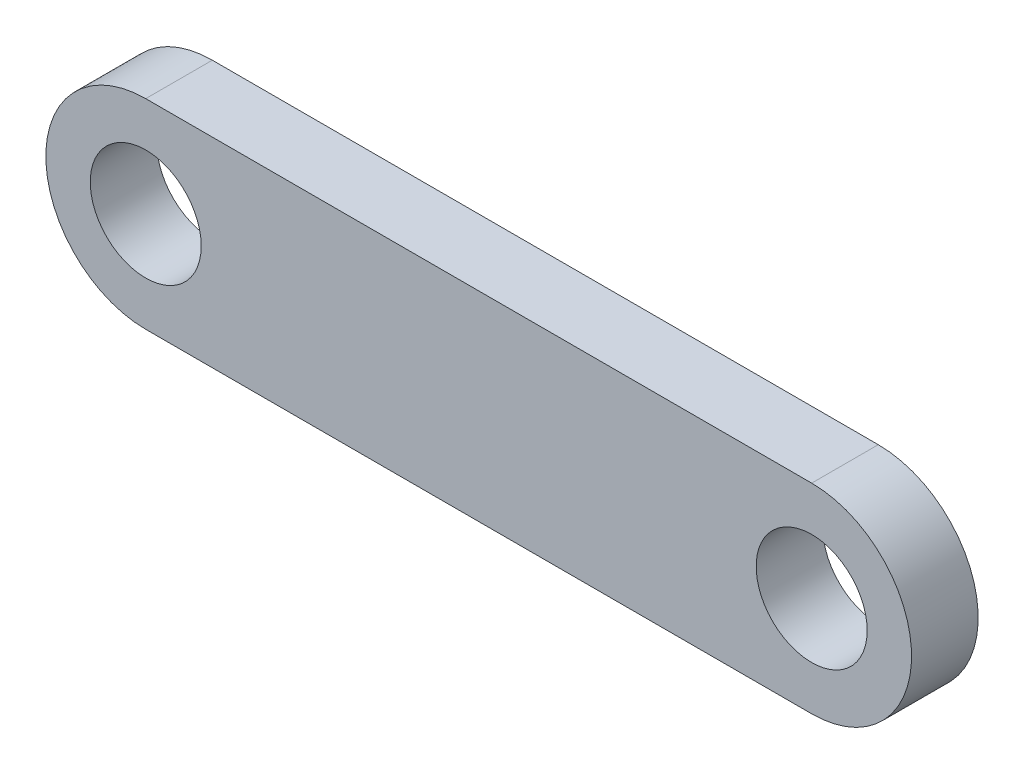
SolidWorks part; units mm, degrees
ref_plane "Alzado" through (0, 0, 0) normal (0, 0, 1) x (1, 0, 0)
ref_plane "Planta" through (0, 0, 0) normal (0, 1, 0) x (1, 0, 0)
ref_plane "Vista lateral" through (0, 0, 0) normal (1, 0, 0) x (0, 0, -1)
sketch "Croquis1" plane through (0, 0, 0) normal (0, 0, 1) x (1, 0, 0)
  line L0 (-22.6795, 0) -> (37.3205, 0) construction
  line L1 (-22.6795, 9) -> (37.3205, 9)
  line L2 (-22.6795, -9) -> (37.3205, -9)
  arc A0 (-22.6795, 9) -> (-22.6795, -9) centre (-22.6795, 0) ccw
  arc A1 (37.3205, -9) -> (37.3205, 9) centre (37.3205, 0) ccw
  circle A2 centre (-22.6795, 0) radius 5
  circle A3 centre (37.3205, 0) radius 5
  point P3 (7.3205, 0)
  dimension "D2" = 10
  dimension "D3" = 9
  dimension "D1" = 60
extrude "Saliente-Extruir1" add sketch "Croquis1" along normal blind 6
